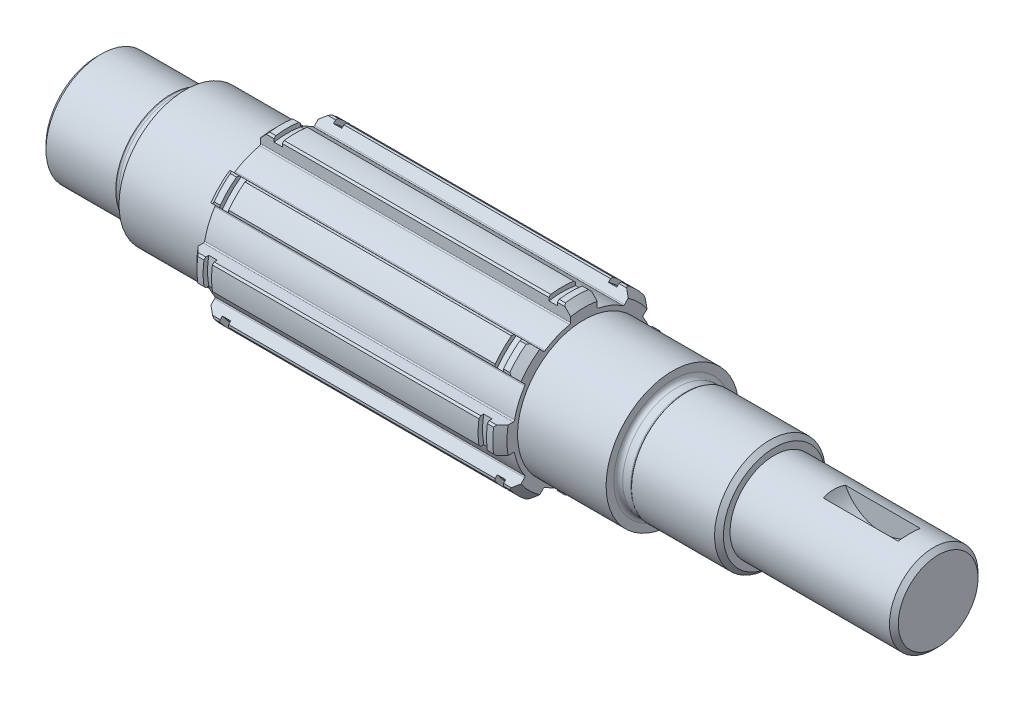
SolidWorks part; units mm, degrees
material "Легированная сталь"
ref_plane "Спереди" through (0, 0, 0) normal (0, 0, 1) x (1, 0, 0)
ref_plane "Сверху" through (0, 0, 0) normal (0, 1, 0) x (1, 0, 0)
ref_plane "Справа" through (0, 0, 0) normal (1, 0, 0) x (0, 0, -1)
sketch "Эскиз 1" plane through (0, 0, 0) normal (0, 0, 1) x (1, 0, 0)
  line L0 (1, 12.5) -> (16.75, 12.5)
  line L1 (20, 15) -> (40, 15)
  line L2 (0, 0) -> (190, 0) construction
  line L3 (133.25, 12.5) -> (152, 12.5)
  line L4 (130, 15) -> (110, 15)
  line L5 (41.6, 19) -> (43, 19)
  line L6 (110, 17.4) -> (110, 15)
  line L7 (189, 10) -> (153, 10)
  line L8 (153, 10) -> (153, 11.5)
  line L9 (1, 12.5) -> (0, 11.5)
  line L10 (189, 10) -> (190, 9)
  line L11 (152, 12.5) -> (153, 11.5)
  line L12 (41.6, 19) -> (40, 17.4)
  line L13 (108.4, 19) -> (110, 17.4)
  line L14 (131, 12.25) -> (132.7929, 12.25)
  line L15 (133.1464, 12.3964) -> (133.25, 12.5)
  line L17 (19, 12.25) -> (17.2071, 12.25)
  line L18 (16.8536, 12.3964) -> (16.75, 12.5)
  line L19 (105.1, 19) -> (105.1, 18)
  line L20 (105.1, 18) -> (107, 18)
  line L21 (107, 18) -> (107, 19)
  line L22 (44.9, 19) -> (44.9, 18)
  line L23 (44.9, 18) -> (43, 18)
  line L24 (43, 18) -> (43, 19)
  line L25 (44.9, 19) -> (105.1, 19)
  line L26 (107, 19) -> (108.4, 19)
  line L27 (130, 13.25) -> (130, 15)
  line L28 (40, 15) -> (40, 17.4)
  line L29 (20, 13.25) -> (20, 15)
  line L30 (0, 11.5) -> (0, 0)
  line L31 (190, 9) -> (190, 0)
  arc A0 (130, 13.25) -> (131, 12.25) centre (131, 13.25) ccw
  arc A1 (132.7929, 12.25) -> (133.1464, 12.3964) centre (132.7929, 12.75) ccw
  arc A2 (19, 12.25) -> (20, 13.25) centre (19, 13.25) ccw
  arc A3 (16.8536, 12.3964) -> (17.2071, 12.25) centre (17.2071, 12.75) ccw
  dimension "D16" = 1
  dimension "D17" = 0.5
  dimension "D31" = 1
  dimension "D33" = 0.5
  dimension "D1" = 25
  dimension "D2" = 190
  dimension "D3" = 30
  dimension "D4" = 38
  dimension "D5" = 20
  dimension "D6" = 25
  dimension "D7" = 30
  dimension "D8" = 20
  dimension "D9" = 20
  dimension "D10" = 70
  dimension "D11" = 20
  dimension "D12" = 60
  dimension "D13" = 37
  dimension "D14" = 1
  dimension "D15" = 1
  dimension "D18" = 3.25
  dimension "D19" = 45
  dimension "D20" = 24.5
  dimension "D21" = 1.6
  dimension "D22" = 1.6
  dimension "D23" = 36
  dimension "D24" = 3
  dimension "D25" = 3
  dimension "D26" = 36
  dimension "D27" = 1.9
  dimension "D28" = 1.9
  dimension "D29" = 1.6
  dimension "D30" = 1.6
  dimension "D32" = 3.25
  dimension "D34" = 45
  dimension "D35" = 1
  dimension "D36" = 1
  dimension "D37" = 1
  dimension "D38" = 1
  dimension "D39" = 24.5
revolve "Повернуть1" add sketch "Эскиз 1" angle 360 about L2
sketch "Эскиз2" plane through (110, 0, 0) normal (1, 0, 0) x (0, 0, -1)
  line L0 (-3, 18.4213) -> (-2.6, 18.8213)
  line L6 (-3, 18.4213) -> (-3, 15.9625)
  line L8 (3, 18.4213) -> (3, 15.9625)
  line L9 (2.6, 18.8213) -> (3, 18.4213)
  line L10 (10.9045, 15.1471) -> (11.4702, 15.1471)
  line L11 (10.9045, 15.1471) -> (9.1658, 13.4085)
  line L12 (15.1471, 10.9045) -> (13.4085, 9.1658)
  line L13 (15.1471, 11.4702) -> (15.1471, 10.9045)
  line L14 (18.4213, 3) -> (18.8213, 2.6)
  line L15 (18.4213, 3) -> (15.9625, 3)
  line L16 (18.4213, -3) -> (15.9625, -3)
  line L17 (18.8213, -2.6) -> (18.4213, -3)
  line L18 (15.1471, -10.9045) -> (15.1471, -11.4702)
  line L19 (15.1471, -10.9045) -> (13.4085, -9.1658)
  line L20 (10.9045, -15.1471) -> (9.1658, -13.4085)
  line L21 (11.4702, -15.1471) -> (10.9045, -15.1471)
  line L22 (3, -18.4213) -> (2.6, -18.8213)
  line L23 (3, -18.4213) -> (3, -15.9625)
  line L24 (-3, -18.4213) -> (-3, -15.9625)
  line L25 (-2.6, -18.8213) -> (-3, -18.4213)
  line L26 (-10.9045, -15.1471) -> (-11.4702, -15.1471)
  line L27 (-10.9045, -15.1471) -> (-9.1658, -13.4085)
  line L28 (-15.1471, -10.9045) -> (-13.4085, -9.1658)
  line L29 (-15.1471, -11.4702) -> (-15.1471, -10.9045)
  line L30 (-18.4213, -3) -> (-18.8213, -2.6)
  line L31 (-18.4213, -3) -> (-15.9625, -3)
  line L32 (-18.4213, 3) -> (-15.9625, 3)
  line L33 (-18.8213, 2.6) -> (-18.4213, 3)
  line L34 (-15.1471, 10.9045) -> (-15.1471, 11.4702)
  line L35 (-15.1471, 10.9045) -> (-13.4085, 9.1658)
  line L36 (-10.9045, 15.1471) -> (-9.1658, 13.4085)
  line L37 (-11.4702, 15.1471) -> (-10.9045, 15.1471)
  arc A1 (-3.2393, 15.6687) -> (3.2393, 15.6687) centre (0, 0) ccw
  arc A2 (-2.6, 18.8213) -> (2.6, 18.8213) centre (0, 0) cw
  arc A3 (-3.2393, 15.6687) -> (-3, 15.9625) centre (-3.3, 15.9625) ccw
  arc A4 (3, 15.9625) -> (3.2393, 15.6687) centre (3.3, 15.9625) ccw
  arc A5 (11.4702, 15.1471) -> (15.1471, 11.4702) centre (0, 0) cw
  arc A6 (8.7889, 13.3699) -> (9.1658, 13.4085) centre (8.9537, 13.6206) ccw
  arc A7 (13.4085, 9.1658) -> (13.3699, 8.7889) centre (13.6206, 8.9537) ccw
  arc A8 (18.8213, 2.6) -> (18.8213, -2.6) centre (0, 0) cw
  arc A9 (15.6687, 3.2393) -> (15.9625, 3) centre (15.9625, 3.3) ccw
  arc A10 (15.9625, -3) -> (15.6687, -3.2393) centre (15.9625, -3.3) ccw
  arc A11 (15.1471, -11.4702) -> (11.4702, -15.1471) centre (0, 0) cw
  arc A12 (13.3699, -8.7889) -> (13.4085, -9.1658) centre (13.6206, -8.9537) ccw
  arc A13 (9.1658, -13.4085) -> (8.7889, -13.3699) centre (8.9537, -13.6206) ccw
  arc A14 (2.6, -18.8213) -> (-2.6, -18.8213) centre (0, 0) cw
  arc A15 (3.2393, -15.6687) -> (3, -15.9625) centre (3.3, -15.9625) ccw
  arc A16 (-3, -15.9625) -> (-3.2393, -15.6687) centre (-3.3, -15.9625) ccw
  arc A17 (-11.4702, -15.1471) -> (-15.1471, -11.4702) centre (0, 0) cw
  arc A18 (-8.7889, -13.3699) -> (-9.1658, -13.4085) centre (-8.9537, -13.6206) ccw
  arc A19 (-13.4085, -9.1658) -> (-13.3699, -8.7889) centre (-13.6206, -8.9537) ccw
  arc A20 (-18.8213, -2.6) -> (-18.8213, 2.6) centre (0, 0) cw
  arc A21 (-15.6687, -3.2393) -> (-15.9625, -3) centre (-15.9625, -3.3) ccw
  arc A22 (-15.9625, 3) -> (-15.6687, 3.2393) centre (-15.9625, 3.3) ccw
  arc A23 (-15.1471, 11.4702) -> (-11.4702, 15.1471) centre (0, 0) cw
  arc A24 (-13.3699, 8.7889) -> (-13.4085, 9.1658) centre (-13.6206, 8.9537) ccw
  arc A25 (-9.1658, 13.4085) -> (-8.7889, 13.3699) centre (-8.9537, 13.6206) ccw
  circle A26 centre (0, 0) radius 19
  point P13 (0, 19)
  point P85 (0, 0)
  circle M17 centre (0, 0) radius 17.4
  dimension "D1" = 6
  dimension "D2" = 19
  dimension "D5" = 32
  dimension "D8" = 0.3
  dimension "D9" = 0.3
  dimension "D4" = 0.4
  dimension "D3" = 0.4
  dimension "D6" = 0.4
  dimension "D7" = 0.4
  dimension "D10" = 8
extrude "Вырез-Вытянуть1" cut sketch "Эскиз2" against normal up to surface (70 mm away) contours L0 A26 L37 L36 L6 M17 | L36 A25 A1 A3 L6 M17 | L34 A26 L33 L32 L35 M17 | A1 A24 L35 L32 A22 M17 | L30 A26 L29 L28 L31 M17 | A1 A21 L31 L28 A19 M17 | A1 A18 L27 L24 A16 M17 | L26 A26 L25 L24 L27 M17 | A1 A15 L23 L20 A13 M17 | L22 A26 L21 L20 L23 M17 | L10 A26 L9 L8 L11 M17 | A1 A6 L11 L8 A4 M17 | L14 A26 L13 L12 L15 M17 | A1 A9 L15 L12 A7 M17 | L18 A26 L17 L16 L19 M17 | A1 A12 L19 L16 A10 M17 up to face at (40, -17.4, 0)
sketch "Эскиз3" plane through (0, 0, 0) normal (0, 0, 1) x (1, 0, 0)
  line L0 (190, -9) -> (190, 9) construction
  circle A0 centre (175, 14) radius 9.5
  point P4 (175, 4.5)
  dimension "D2" = 19
  dimension "D1" = 15
  dimension "D3" = 5.5
extrude "Вырез-Вытянуть2" cut sketch "Эскиз3" against normal blind 2.5 and the other way blind 2.5 contours A0
